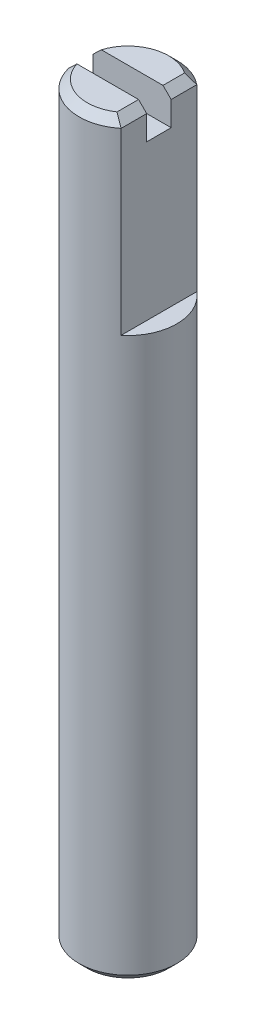
SolidWorks part; units mm, degrees
ref_plane "Vorne" through (0, 0, 0) normal (0, 0, 1) x (1, 0, 0)
ref_plane "Oben" through (0, 0, 0) normal (0, 1, 0) x (1, 0, 0)
ref_plane "Rechts" through (0, 0, 0) normal (1, 0, 0) x (0, 0, -1)
sketch "Skizze1" plane through (0, 0, 0) normal (0, 1, 0) x (1, 0, 0)
  circle A0 centre (0, 0) radius 3
  dimension "D1" = 6
extrude "Aufsatz-Linear austragen1" add sketch "Skizze1" along normal blind 46
cosmetic thread "Gewindedarstellung1" parameters "D2"=5
sketch "Skizze2" plane through (0, 46, 0) normal (0, 1, 0) x (1, 0, 0)
  line L0 (0, -3.3) -> (0, 3.3) construction
  line L1 (1.9, 3.8045) -> (4.1212, 3.8045)
  line L2 (1.9, 3.8045) -> (1.9, -4.947)
  line L3 (1.9, -4.947) -> (4.1212, -4.947)
  line L4 (4.1212, 3.8045) -> (4.1212, -4.947)
  dimension "D1" = 1.9
extrude "Schnitt-Linear austragen1" cut sketch "Skizze2" against normal blind 11.5
chamfer "Fase1" distance 0.5 angle 45 3 edges at (-3, 46, 0) (0, 0, 3) (1.9, 46, 0)
sketch "Skizze3" plane through (0, 46, 0) normal (0, 1, 0) x (1, 0, 0)
  line L1 (-4.2045, 0.75) -> (0.75, 0.75)
  line L2 (-4.2045, 0.75) -> (-4.2045, -0.75)
  line L3 (-4.2045, -0.75) -> (0.75, -0.75)
  line L4 (4.6066, 0.75) -> (4.6066, -0.75)
  line L9 (-3.3, 0) -> (3.3, 0) construction
  line L10 (0.75, 0.75) -> (4.6066, 0.75)
  line L12 (0.75, -0.75) -> (4.6066, -0.75)
  dimension "D1" = 1.5
  dimension "D4" = 0.75
extrude "Schnitt-Linear austragen2" cut sketch "Skizze3" against normal blind 2
